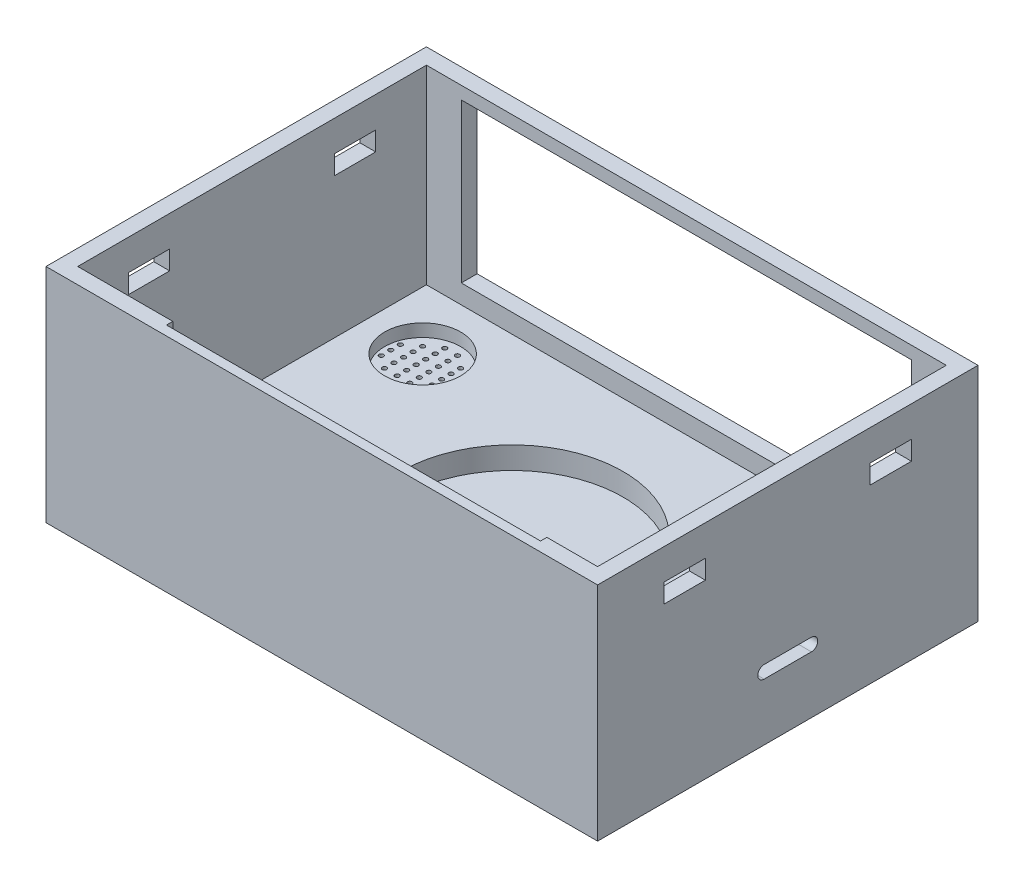
SolidWorks part; units mm, degrees
ref_plane "Front Plane" through (0, 0, 0) normal (0, 0, 1) x (1, 0, 0)
ref_plane "Top Plane" through (0, 0, 0) normal (0, 1, 0) x (1, 0, 0)
ref_plane "Right Plane" through (0, 0, 0) normal (1, 0, 0) x (0, 0, -1)
sketch "Sketch1" plane through (0, 0, 0) normal (0, 1, 0) x (1, 0, 0)
  line L1 (-36.9703, 36.4301) -> (50.0297, 36.4301)
  line L2 (-36.9703, 36.4301) -> (-36.9703, -23.5699)
  line L3 (-36.9703, -23.5699) -> (50.0297, -23.5699)
  line L4 (50.0297, 36.4301) -> (50.0297, -23.5699)
  dimension "D1" = 60
  dimension "D2" = 87
extrude "Housing" add sketch "Sketch1" along normal blind 35
sketch "Sketch4" plane through (0, 35, 0) normal (0, 1, 0) x (1, 0, 0)
  line L0 (-36.9703, 36.4301) -> (-36.9703, -23.5699) construction
  line L1 (-34.4703, 33.9301) -> (47.5297, 33.9301)
  line L2 (-34.4703, 33.9301) -> (-34.4703, -21.0699)
  line L3 (-34.4703, -21.0699) -> (47.5297, -21.0699)
  line L4 (47.5297, 33.9301) -> (47.5297, -21.0699)
  line L5 (50.0297, 36.4301) -> (-36.9703, 36.4301) construction
  dimension "D1" = 55
  dimension "D2" = 82
  dimension "D3" = 2.5
  dimension "D4" = 2.5
extrude "HouseInternalCut" cut sketch "Sketch4" against normal blind 30
sketch "Sketch6" plane through (-29.4597, 5, 17.6787) normal (0, 1, 0) x (1, 0, 0)
  line L1 (2.5049, 12.2395) -> (6.2049, 12.2395)
  line L2 (2.5049, 12.2395) -> (2.5049, 3.7395)
  line L3 (2.5049, 3.7395) -> (6.2049, 3.7395)
  line L4 (6.2049, 12.2395) -> (6.2049, 3.7395)
  dimension "D1" = 3.7
  dimension "D2" = 8.5
extrude "SwitchExternalCut" cut sketch "Sketch6" against normal blind 2
sketch "Sketch8" plane through (-29.4597, 3, 17.6787) normal (0, 1, 0) x (1, 0, 0)
  line L0 (2.5049, 3.7395) -> (6.2049, 3.7395) construction
  line L1 (3.5049, 9.7895) -> (5.2049, 9.7895)
  line L2 (3.5049, 9.7895) -> (3.5049, 6.1895)
  line L3 (3.5049, 6.1895) -> (5.2049, 6.1895)
  line L4 (5.2049, 9.7895) -> (5.2049, 6.1895)
  line L5 (6.2049, 12.2395) -> (2.5049, 12.2395) construction
  line L7 (2.5049, 12.2395) -> (2.5049, 3.7395) construction
  dimension "D1" = 1.7
  dimension "D2" = 3.6
  dimension "D3" = 2.45
  dimension "D4" = 2.45
  dimension "D5" = 1
extrude "SwitchInternalCut" cut sketch "Sketch8" against normal through all
sketch "Sketch10" plane through (-0.3149, 5, -24.1886) normal (0, 1, 0) x (1, 0, 0)
  circle A0 centre (-25.0066, 0) radius 6
  dimension "D1" = 12
extrude "BuzzerExternalCut" cut sketch "Sketch10" against normal blind 2
sketch "Sketch12" plane through (-0.3149, 3, -24.1886) normal (0, 1, 0) x (1, 0, 0)
  circle A0 centre (-26.0423, 4.5223) radius 0.35
  circle A1 centre (-26.0423, 3.0204) radius 0.35
  circle A2 centre (-26.0423, 1.5185) radius 0.35
  circle A3 centre (-26.0423, 0.0167) radius 0.35
  circle A4 centre (-26.0423, -1.4852) radius 0.35
  circle A5 centre (-26.0423, -2.9871) radius 0.35
  circle A6 centre (-26.0423, -4.489) radius 0.35
  circle A7 centre (-24.0423, 4.5223) radius 0.35
  circle A8 centre (-24.0423, 3.0204) radius 0.35
  circle A9 centre (-22.0423, 3.0204) radius 0.35
  circle A10 centre (-28.0423, 3.0204) radius 0.35
  circle A11 centre (-24.0423, 1.5185) radius 0.35
  circle A12 centre (-22.0423, 1.5185) radius 0.35
  circle A13 centre (-20.0423, 1.5185) radius 0.35
  circle A14 centre (-28.0423, 1.5185) radius 0.35
  circle A15 centre (-30.0423, 1.5185) radius 0.35
  circle A16 centre (-24.0423, 0.0167) radius 0.35
  circle A17 centre (-22.0423, 0.0167) radius 0.35
  circle A18 centre (-20.0423, 0.0167) radius 0.35
  circle A19 centre (-24.0423, -1.4852) radius 0.35
  circle A20 centre (-22.0423, -1.4852) radius 0.35
  circle A21 centre (-20.0423, -1.4852) radius 0.35
  circle A22 centre (-24.0423, -2.9871) radius 0.35
  circle A23 centre (-22.0423, -2.9871) radius 0.35
  circle A24 centre (-24.0423, -4.489) radius 0.35
  circle A25 centre (-28.0423, -2.9871) radius 0.35
  circle A26 centre (-28.0423, -1.4852) radius 0.35
  circle A27 centre (-30.0423, -1.4852) radius 0.35
  circle A28 centre (-28.0423, 0.0167) radius 0.35
  circle A29 centre (-30.0423, 0.0167) radius 0.35
  dimension "D1" = 0.7
  dimension "D2" = 7
  dimension "D3" = 2
  dimension "D4" = 3
  dimension "D5" = 2
  dimension "D6" = 4
  dimension "D7" = 3
  dimension "D8" = 4
  dimension "D9" = 4
  dimension "D10" = 3
  dimension "D11" = 2
  dimension "D12" = 2
  dimension "D13" = 3
  dimension "D14" = 3
extrude "BuzzerInternalCut" cut sketch "Sketch12" against normal through all contours A7 | A1 | A10 | A15 | A29 | A27 | A28 | A14 | A26 | A25 | A3 | A2 | A4 | A5 | A6 | A24 | A22 | A19 | A16 | A11 | A8 | A9 | A12 | A17 | A20 | A23 | A21 | A18 | A13 | A0
sketch "Sketch14" plane through (-24.2277, 5, -14.724) normal (0, 1, 0) x (1, 0, 0)
  line L1 (-3.3963, -7.5527) -> (1.2037, -7.5527)
  line L2 (-3.3963, -7.5527) -> (-3.3963, -13.6527)
  line L3 (-3.3963, -13.6527) -> (1.2037, -13.6527)
  line L4 (1.2037, -7.5527) -> (1.2037, -13.6527)
  dimension "D1" = 6.1
  dimension "D2" = 4.6
extrude "ButtonExternalCut" cut sketch "Sketch14" against normal blind 2
sketch "Sketch16" plane through (-24.2277, 3, -14.724) normal (0, 1, 0) x (1, 0, 0)
  circle A0 centre (-1.0963, -10.6027) radius 1.5
  dimension "D1" = 3
  dimension "D2" = 2.3
  dimension "D3" = 3.05
extrude "ButtonInternalCut" cut sketch "Sketch16" against normal through all
sketch "Sketch29" plane through (0, 5, 0) normal (0, 1, 0) x (1, 0, 0)
  line L0 (-34.4703, -21.0699) -> (47.5297, -21.0699) construction
  line L1 (-36.9703, 36.4301) -> (-36.9703, -23.5699) construction
  line L2 (47.5297, -21.0699) -> (47.5297, 33.9301) construction
  line L3 (50.0297, -23.5699) -> (50.0297, 36.4301) construction
  line L4 (-36.9703, -23.5699) -> (50.0297, -23.5699) construction
  circle A0 centre (6.5297, 6.4301) radius 17.515
  point P8 (0, 0)
  dimension "D1" = 35.03
  dimension "D4" = 41
  dimension "D2" = 27.5
  dimension "D3" = 43.5
  dimension "D5" = 43.5
  dimension "D6" = 30
extrude "WiChargeCut" cut sketch "Sketch29" against normal blind 3.5
sketch "Sketch30" plane through (0, 0, 21.0699) normal (0, 0, -1) x (-1, 0, 0)
  line L0 (-47.5297, 5) -> (-47.5297, 35) construction
  line L1 (19.4703, 45) -> (-39.5297, 45)
  line L2 (19.4703, 45) -> (19.4703, 6)
  line L3 (19.4703, 6) -> (-39.5297, 6)
  line L4 (-39.5297, 45) -> (-39.5297, 6)
  line L5 (34.4703, 5) -> (-47.5297, 5) construction
  dimension "D1" = 39
  dimension "D2" = 59
  dimension "D3" = 8
  dimension "D4" = 1
extrude "RFIDModuleCut" cut sketch "Sketch30" against normal blind 1
sketch "Sketch32" plane through (0, 0, -33.9301) normal (0, 0, 1) x (1, 0, 0)
  line L0 (-34.4703, 5) -> (-34.4703, 35) construction
  line L1 (-28.9703, 33) -> (42.0297, 33)
  line L2 (-28.9703, 33) -> (-28.9703, 8)
  line L3 (-28.9703, 8) -> (42.0297, 8)
  line L4 (42.0297, 33) -> (42.0297, 8)
  line L5 (47.5297, 5) -> (-34.4703, 5) construction
  line L6 (47.5297, 5) -> (47.5297, 35) construction
  dimension "D1" = 71
  dimension "D2" = 25
  dimension "D3" = 5.5
  dimension "D4" = 3
  dimension "D5" = 5.5
extrude "DisplayCut" cut sketch "Sketch32" against normal through all
sketch "Sketch33" plane through (50.0297, 0, 0) normal (1, 0, 0) x (0, 0, -1)
  line L0 (2.7051, 10) -> (10.1551, 10) construction
  line L1 (2.7051, 11) -> (10.1551, 11)
  line L2 (2.7051, 9) -> (10.1551, 9)
  line L3 (-23.5699, 35) -> (-23.5699, 0) construction
  line L5 (-23.5699, 0) -> (36.4301, 0) construction
  arc A0 (2.7051, 11) -> (2.7051, 9) centre (2.7051, 10) ccw
  arc A1 (10.1551, 9) -> (10.1551, 11) centre (10.1551, 10) ccw
  point P2 (6.4301, 10)
  dimension "D1" = 7.45
  dimension "D2" = 2
  dimension "D3" = 30
  dimension "D4" = 10
extrude "MicroUSBCut" cut sketch "Sketch33" against normal blind 2.5
sketch "Sketch34" plane through (-36.9703, 0, 0) normal (-1, 0, 0) x (0, 0, 1)
  line L0 (-36.4301, 35) -> (-36.4301, 0) construction
  line L1 (-25.9301, 30.1475) -> (-19.4301, 30.1475)
  line L2 (-25.9301, 30.1475) -> (-25.9301, 27.1475)
  line L3 (-25.9301, 27.1475) -> (-19.4301, 27.1475)
  line L4 (-19.4301, 30.1475) -> (-19.4301, 27.1475)
  line L5 (6.5699, 30.1475) -> (6.5699, 27.1475)
  line L6 (6.5699, 30.1475) -> (13.0699, 30.1475)
  line L7 (13.0699, 30.1475) -> (13.0699, 27.1475)
  line L8 (6.5699, 27.1475) -> (13.0699, 27.1475)
  line L9 (23.5699, 35) -> (23.5699, 0) construction
  dimension "D1" = 3
  dimension "D2" = 6.5
  dimension "D3" = 10.5
  dimension "D5" = 10.5
  dimension "D4" = 2
extrude "ClipsCut" cut sketch "Sketch34" against normal through all
sketch "Sketch35" plane through (0, 5, 0) normal (0, 1, 0) x (1, 0, 0)
  line L1 (-28.9703, 33.9301) -> (42.0297, 33.9301) construction
  line L2 (47.5297, -21.0699) -> (47.5297, 33.9301) construction
  circle A0 centre (46.5297, -2.5099) radius 0.45
  dimension "D1" = 0.9
  dimension "D2" = 36.44
  dimension "D3" = 1
extrude "ResetCut" cut sketch "Sketch35" against normal through all
